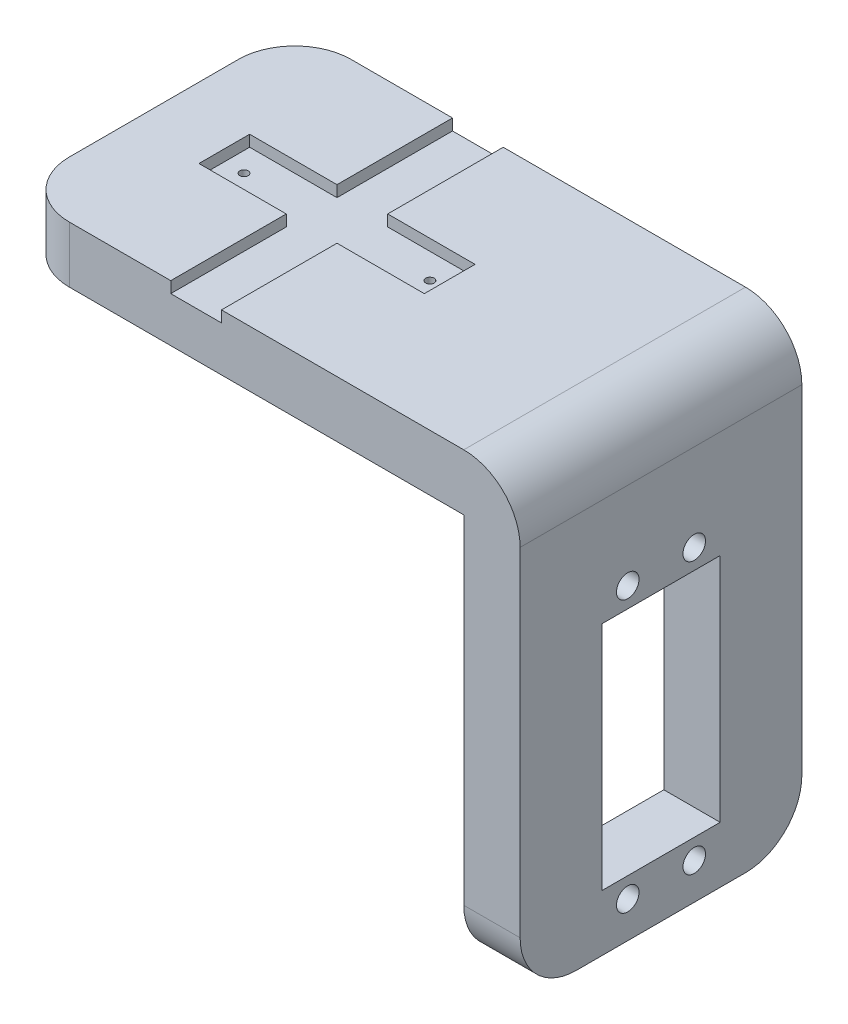
SolidWorks part; units mm, degrees
ref_plane "Front Plane" through (0, 0, 0) normal (0, 0, 1) x (1, 0, 0)
ref_plane "Top Plane" through (0, 0, 0) normal (0, 1, 0) x (1, 0, 0)
ref_plane "Right Plane" through (0, 0, 0) normal (1, 0, 0) x (0, 0, -1)
sketch "Sketch1" plane through (0, 0, 0) normal (0, 1, 0) x (1, 0, 0)
  line L1 (-21.4484, 6.5781) -> (38.5516, 6.5781)
  line L2 (-21.4484, 6.5781) -> (-21.4484, -43.4219)
  line L3 (-21.4484, -43.4219) -> (38.5516, -43.4219)
  line L4 (38.5516, 6.5781) -> (38.5516, -43.4219)
  dimension "D1" = 60
  dimension "D2" = 50
extrude "Boss-Extrude1" add sketch "Sketch1" along normal blind 10
sketch "Sketch3" plane through (-21.4484, 0, 0) normal (-1, 0, 0) x (0, 0, 1)
  line L1 (-6.5781, 0) -> (43.4219, 0)
  line L2 (-6.5781, 0) -> (-6.5781, 10)
  line L3 (-6.5781, 10) -> (43.4219, 10)
  line L4 (43.4219, 0) -> (43.4219, 10)
extrude "Boss-Extrude2" add sketch "Sketch3" along normal blind 20
sketch "Sketch2" plane through (0, 10, 0) normal (0, 1, 0) x (1, 0, 0)
  line L0 (38.5516, -18.4219) -> (7.5516, -18.4219) construction
  line L1 (38.5516, -43.4219) -> (38.5516, 6.5781) construction
  line L2 (7.5516, -18.4219) -> (-8.9484, -18.4219) construction
  line L3 (-8.9484, -18.4219) -> (-25.4484, -18.4219) construction
  line L4 (-8.9484, -18.4219) -> (-8.9484, -22.9219) construction
  line L10 (-8.9484, -22.9219) -> (-28.9484, -22.9219)
  line L11 (-8.9484, -22.9219) -> (-8.9484, -13.9219)
  line L12 (-8.9484, -13.9219) -> (-28.9484, -13.9219)
  line L13 (-28.9484, -22.9219) -> (-28.9484, -13.9219)
  point P10 (0, 0)
  dimension "D1" = 31
  dimension "D2" = 16.5
  dimension "D3" = 16.5
  dimension "D4" = 4.5
  dimension "D5" = 20
  dimension "D6" = 9
extrude "Cut-Extrude2" cut sketch "Sketch2" against normal blind 2
mirror "Mirror6" about plane through (-8.9484, 8, 22.9219) normal (1, 0, 0) of "Cut-Extrude2"
ref_plane "Plane3" through (-8.9484, 0, 0) normal (1, 0, 0) x (0, 0, -1)
sketch "Sketch5" plane through (0, 10, 0) normal (0, 1, 0) x (1, 0, 0)
  line L0 (-8.9484, -13.9219) -> (-4.4484, -13.9219) construction
  line L1 (11.0516, -13.9219) -> (-28.9484, -13.9219) construction
  line L2 (38.5516, 6.5781) -> (-41.4484, 6.5781) construction
  line L3 (-4.4484, -13.9219) -> (-13.4484, -13.9219)
  line L4 (-4.4484, -13.9219) -> (-4.4484, 6.5781)
  line L5 (-4.4484, 6.5781) -> (-13.4484, 6.5781)
  line L6 (-13.4484, -13.9219) -> (-13.4484, 6.5781)
  dimension "D1" = 4.5
  dimension "D2" = 9
extrude "Cut-Extrude3" cut sketch "Sketch5" against normal blind 2
ref_plane "Plane4" through (0, 0, 18.4219) normal (0, 0, 1) x (1, 0, 0)
mirror "Mirror7" about plane through (0, 0, 18.4219) normal (0, 0, 1) of "Cut-Extrude3"
sketch "Sketch6" plane through (0, 8, 0) normal (0, 1, 0) x (1, 0, 0)
  line L0 (-13.4484, -22.9219) -> (-13.4484, -18.4219) construction
  line L1 (-13.4484, -18.4219) -> (-25.4484, -18.4219) construction
  circle A0 centre (-25.4484, -18.4219) radius 0.75
  dimension "D2" = 4.5
  dimension "D1" = 12
extrude "Cut-Extrude4" cut sketch "Sketch6" against normal through all
mirror "Mirror8" about plane through (-8.9484, 0, 0) normal (1, 0, 0) of "Cut-Extrude4"
sketch "Sketch9" plane through (0, 10, 0) normal (0, 1, 0) x (1, 0, 0)
  line L1 (38.5516, 6.5781) -> (48.5516, 6.5781)
  line L2 (38.5516, 6.5781) -> (38.5516, -43.4219)
  line L3 (38.5516, -43.4219) -> (48.5516, -43.4219)
  line L4 (48.5516, 6.5781) -> (48.5516, -43.4219)
  dimension "D1" = 50
  dimension "D2" = 10
extrude "Boss-Extrude3" add sketch "Sketch9" against normal blind 80
fillet "Fillet1" radius 10 1 edges at (48.5516, 10, 18.4219)
fillet "Fillet2" radius 10 1 edges at (-41.4484, 5, -6.5781)
fillet "Fillet3" radius 10 1 edges at (-41.4484, 5, 43.4219)
fillet "Fillet4" radius 10 1 edges at (43.5516, -70, 43.4219)
fillet "Fillet5" radius 10 1 edges at (43.5516, -70, -6.5781)
sketch "Sketch11" plane through (38.5516, 0, 0) normal (-1, 0, 0) x (0, 0, 1)
  line L0 (18.4219, -70) -> (18.4219, -60) construction
  line L1 (3.4219, -70) -> (33.4219, -70) construction
  line L3 (18.4219, -60) -> (7.9219, -60)
  line L4 (18.4219, -60) -> (18.4219, -19)
  line L5 (18.4219, -19) -> (7.9219, -19)
  line L6 (7.9219, -60) -> (7.9219, -19)
  dimension "D1" = 10
  dimension "D2" = 41
  dimension "D3" = 10.5
extrude "Cut-Extrude5" cut sketch "Sketch11" against normal blind 40
mirror "Mirror9" about plane through (78.5516, -60, 18.4219) normal (0, 0, 1) of "Cut-Extrude5"
sketch "Sketch13" plane through (38.5516, 0, 0) normal (-1, 0, 0) x (0, 0, 1)
  line L0 (18.4219, -60) -> (18.4219, -63.56) construction
  line L1 (7.9219, -60) -> (28.9219, -60) construction
  line L2 (18.4219, -63.56) -> (12.5219, -63.56) construction
  circle A0 centre (12.5219, -63.56) radius 2
  dimension "D1" = 5.9
  dimension "D2" = 3.56
extrude "Cut-Extrude6" cut sketch "Sketch13" against normal blind 40
ref_plane "Plane11" through (0, -39.5, 0) normal (0, 1, 0) x (1, 0, 0)
ref_plane "Plane12" through (0, 0, 18.4219) normal (0, 0, 1) x (1, 0, 0)
mirror "Mirror10" about plane through (0, 0, 18.4219) normal (0, 0, 1) of "Cut-Extrude6"
mirror "Mirror11" about plane through (0, -39.5, 0) normal (0, 1, 0) of "Mirror10", "Cut-Extrude6"
